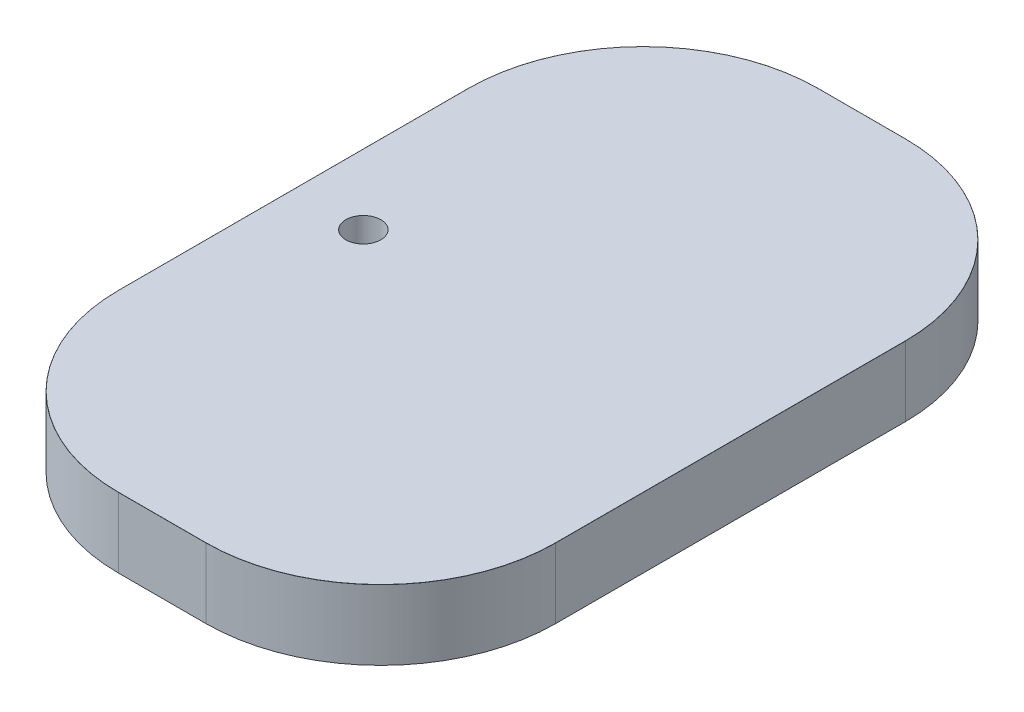
SolidWorks part; units mm, degrees
ref_plane "Alzado" through (0, 0, 0) normal (0, 0, 1) x (1, 0, 0)
ref_plane "Planta" through (0, 0, 0) normal (0, 1, 0) x (1, 0, 0)
ref_plane "Vista lateral" through (0, 0, 0) normal (1, 0, 0) x (0, 0, -1)
sketch "Croquis2" plane through (0, 0, 0) normal (0, 1, 0) x (1, 0, 0)
  line L0 (-5, 40) -> (5, 40)
  line L1 (25, 20) -> (25, -20)
  line L2 (-5, -40) -> (5, -40)
  line L3 (-25, -20) -> (-25, 20)
  arc A0 (5, 40) -> (25, 20) centre (5, 20) cw
  arc A1 (25, -20) -> (5, -40) centre (5, -20) cw
  arc A2 (-5, -40) -> (-25, -20) centre (-5, -20) cw
  arc A3 (-25, 20) -> (-5, 40) centre (-5, 20) cw
  point P12 (0, 40)
  point P14 (25, 0)
  point P15 (0, 0)
  point P16 (0, 0)
  point P17 (0, 0)
  point P18 (0, 0)
  point P19 (13.6087, 40)
  dimension "D3" = 20
  dimension "D1" = 50
  dimension "D2" = 80
extrude "Saliente-Extruir1" add sketch "Croquis2" along normal blind 8
fillet "Redondeo1" radius 0.01 8 edges at (-19.1421, 8, -34.1421) (0, 8, -40) (19.1421, 8, -34.1421) (25, 8, 0) (19.1421, 8, 34.1421) (0, 8, 40) (-19.1421, 8, 34.1421) (-25, 8, 0)
sketch "Croquis3" plane through (0, 8, 0) normal (0, 1, 0) x (1, 0, 0)
  line L1 (-25, -20) -> (-25, 20) construction
  circle A1 centre (-17, 0) radius 2
  point P4 (0, 0)
  point P5 (-17, 0)
  point P6 (-19, 0)
  point P7 (0, 0)
  dimension "D1" = 8
  dimension "D2" = 4
extrude "Cortar-Extruir1" cut sketch "Croquis3" against normal blind 6
sketch "Croquis4" plane through (0, 8, 0) normal (0, 1, 0) x (1, 0, 0)
  circle A0 centre (-17, 0) radius 1.25
  dimension "D1" = 2.5
extrude "Cortar-Extruir2" cut sketch "Croquis4" against normal blind 10
